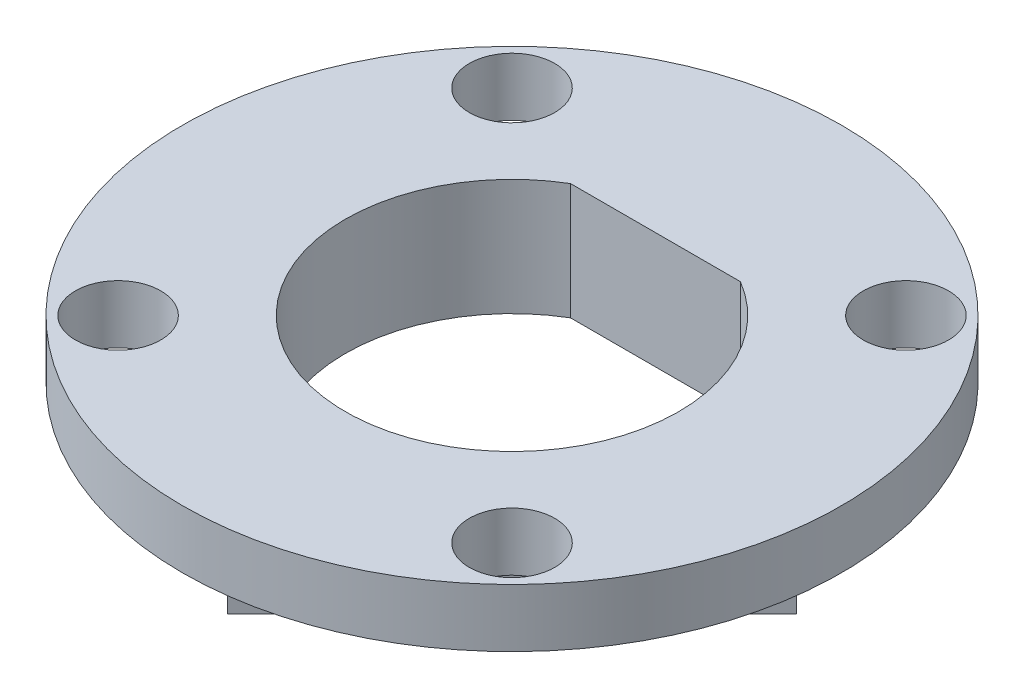
SolidWorks part; units mm, degrees
ref_plane "Front Plane" through (0, 0, 0) normal (0, 0, 1) x (1, 0, 0)
ref_plane "Top Plane" through (0, 0, 0) normal (0, 1, 0) x (1, 0, 0)
ref_plane "Right Plane" through (0, 0, 0) normal (1, 0, 0) x (0, 0, -1)
sketch "스케치1" plane through (0, 0, 0) normal (0, 1, 0) x (1, 0, 0)
  circle A0 centre (0, 0) radius 8.5
extrude "보스-돌출1" add sketch "스케치1" along normal blind 3
sketch "스케치2" plane through (0, 3, 0) normal (0, 1, 0) x (1, 0, 0)
  line L0 (0, 0.6273) -> (0, 50000.6273) construction
  line L1 (-2.1569, 3.7) -> (49997.8431, 3.7) construction
  line L2 (0, -4.3) -> (50000, -4.3) construction
  line L3 (1.1885, 0) -> (50001.1885, 0) construction
  line L4 (-2.1909, 3.7) -> (2.1909, 3.7)
  circle A0 centre (0, 0) radius 4.3 construction
  arc A1 (-2.1909, 3.7) -> (2.1909, 3.7) centre (0, 0) ccw
  dimension "D2" = 4.3
  dimension "D3" = 3.7
extrude "컷-돌출1" cut sketch "스케치2" against normal blind 3
sketch "스케치3" plane through (0, 3, 0) normal (0, 1, 0) x (1, 0, 0)
  line L0 (0, 0) -> (0, 50000) construction
  line L1 (-2.54, -0.055) -> (-2.54, 49999.945) construction
  line L2 (2.54, -0.1869) -> (2.54, 49999.8131) construction
  line L3 (-5.08, -0.2088) -> (-5.08, 49999.7912) construction
  line L4 (-7.62, -0.3187) -> (-7.62, 49999.6813) construction
  line L5 (5.08, -0.3407) -> (5.08, 49999.6593) construction
  line L6 (7.62, -0.1869) -> (7.62, 49999.8131) construction
  line L7 (0, 0) -> (50000, 0) construction
  line L8 (0, 2.54) -> (50000, 2.54) construction
  line L9 (0, 5.08) -> (50000, 5.08) construction
  line L10 (0, -2.54) -> (50000, -2.54) construction
  line L11 (0, -5.08) -> (50000, -5.08) construction
  line L12 (0, -7.62) -> (50000, -7.62) construction
  line L13 (0, 7.62) -> (50000, 7.62) construction
  circle A0 centre (5.08, 5.08) radius 1.1
  circle A1 centre (-5.08, -5.08) radius 1.1
  circle A2 centre (5.08, -5.08) radius 1.1
  circle A3 centre (-5.08, 5.08) radius 1.1
  dimension "D1" = 2.54
  dimension "D2" = 2.54
  dimension "D3" = 2.54
  dimension "D4" = 2.54
  dimension "D5" = 2.54
  dimension "D6" = 2.54
  dimension "D7" = 2.54
  dimension "D8" = 2.54
  dimension "D9" = 2.54
  dimension "D10" = 2.54
  dimension "D11" = 2.54
  dimension "D12" = 2.54
extrude "컷-돌출2" cut sketch "스케치3" against normal blind 3
sketch "스케치4" plane through (0, 0, 0) normal (0, -1, 0) x (1, 0, 0)
  line L0 (-5.08, 5.08) -> (-5.08, -49994.92) construction
  line L1 (5.08, 5.08) -> (5.08, -49994.92) construction
  line L2 (-5.08, -5.08) -> (49994.92, -5.08) construction
  line L3 (-5.08, 5.08) -> (49994.92, 5.08) construction
  line L4 (-5.08, 5.08) -> (35350.2591, 35360.4191) construction
  line L5 (1.0973, 8.4289) -> (-8.4289, -1.0973)
  line L8 (-4.3747, 2.9568) -> (35350.9643, 35358.2959) construction
  circle A0 centre (0, 0) radius 8.5 construction
  arc A1 (-8.4289, -1.0973) -> (1.0973, 8.4289) centre (0, 0) cw
  dimension "D1" = 45
  dimension "D2" = 2
extrude "컷-돌출3" cut sketch "스케치4" against normal blind 1.5
pattern_circular "원형 패턴1" count 4 every 90 about axis through (0, 0, 0) along (0, 1, 0) of "컷-돌출3"
